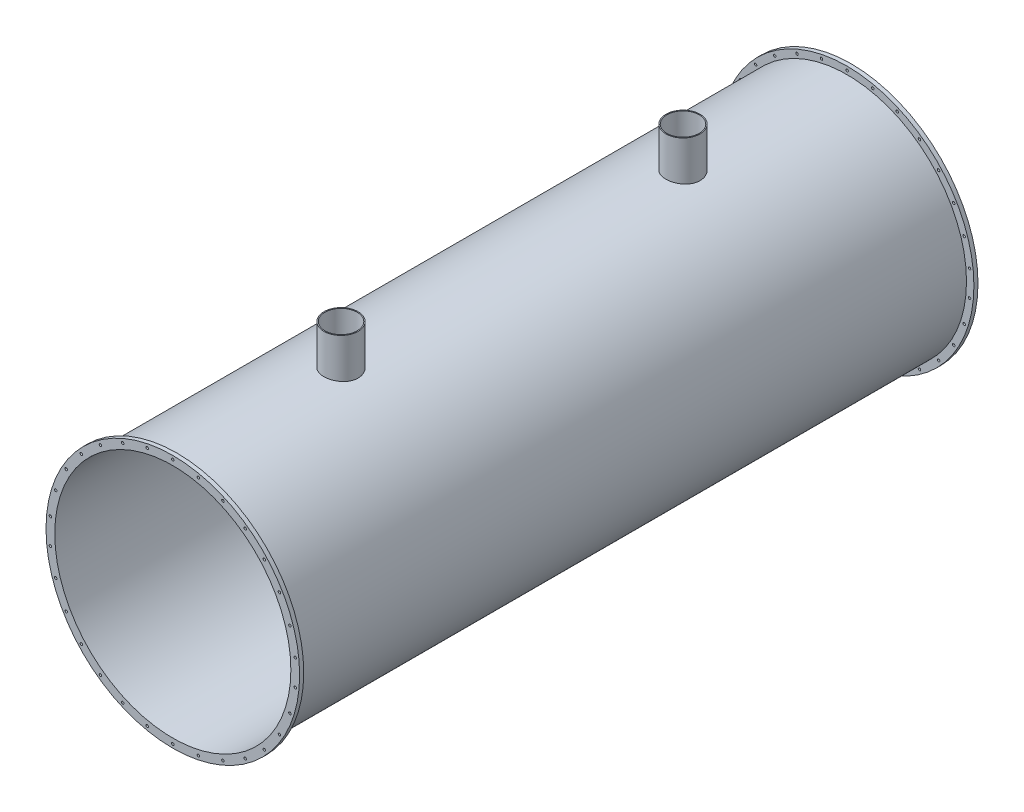
SolidWorks part; units mm, degrees
ref_plane "Front Plane" through (0, 0, 0) normal (0, 0, 1) x (1, 0, 0)
ref_plane "Top Plane" through (0, 0, 0) normal (0, 1, 0) x (1, 0, 0)
ref_plane "Right Plane" through (0, 0, 0) normal (1, 0, 0) x (0, 0, -1)
sketch "Sketch1" plane through (0, 0, 0) normal (0, 0, 1) x (1, 0, 0)
  circle A0 centre (0, 0) radius 2130.025
  circle A1 centre (0, 0) radius 2105.58
extrude "Boss-Extrude1" add sketch "Sketch1" along normal blind 12100
ref_plane "Plane1" through (0, 2830.0235, 0) normal (0, 1, 0) x (1, 0, 0)
sketch "Sketch2" plane through (0, 2830.0235, 0) normal (0, 1, 0) x (1, 0, 0)
  line L0 (2130.025, 0) -> (-2130.025, 0) construction
  line L1 (-2130.025, -12100) -> (2130.025, -12100) construction
  circle A0 centre (0, -3000) radius 304.8
  circle A1 centre (0, -9100) radius 304.8
  dimension "D1" = 609.6
  dimension "D3" = 3000
  dimension "D2" = 3000
extrude "Boss-Extrude2" add sketch "Sketch2" against normal up to surface up to face at (2130.025, 0, 12100)
sketch "Sketch3" plane through (0, 2830.0235, 0) normal (0, 1, 0) x (1, 0, 0)
  circle A0 centre (0, -9100) radius 287.4
  circle A1 centre (0, -3000) radius 287.4
  dimension "D1" = 574.8
extrude "Cut-Extrude1" cut sketch "Sketch3" against normal blind 1000
sketch "Sketch4" plane through (0, 0, 12100) normal (0, 0, 1) x (1, 0, 0)
  circle A0 centre (0, 0) radius 2262.0235
  circle A1 centre (0, 0) radius 2130.025 construction
  circle A2 centre (0, 0) radius 2130.025
  dimension "D1" = 4524.047
extrude "Boss-Extrude3" add sketch "Sketch4" against normal blind 73
sketch "Sketch5" plane through (0, 0, 12100) normal (0, 0, 1) x (1, 0, 0)
  circle A0 centre (0, 0) radius 2196.025 construction
  circle A1 centre (0, 2196.025) radius 22
  circle A2 centre (456.5793, 2148.0366) radius 22
  circle A3 centre (893.2038, 2006.1687) radius 22
  circle A4 centre (1290.7911, 1776.6215) radius 22
  circle A5 centre (1631.9646, 1469.4275) radius 22
  circle A6 centre (1901.8134, 1098.0125) radius 22
  circle A7 centre (2088.5439, 678.609) radius 22
  circle A8 centre (2183.9949, 229.5471) radius 22
  circle A9 centre (2183.9949, -229.5471) radius 22
  circle A10 centre (2088.5439, -678.609) radius 22
  circle A11 centre (1901.8134, -1098.0125) radius 22
  circle A12 centre (1631.9646, -1469.4275) radius 22
  circle A13 centre (1290.7911, -1776.6215) radius 22
  circle A14 centre (893.2038, -2006.1687) radius 22
  circle A15 centre (456.5793, -2148.0366) radius 22
  circle A16 centre (0, -2196.025) radius 22
  circle A17 centre (-456.5793, -2148.0366) radius 22
  circle A18 centre (-893.2038, -2006.1687) radius 22
  circle A19 centre (-1290.7911, -1776.6215) radius 22
  circle A20 centre (-1631.9646, -1469.4275) radius 22
  circle A21 centre (-1901.8134, -1098.0125) radius 22
  circle A22 centre (-2088.5439, -678.609) radius 22
  circle A23 centre (-2183.9949, -229.5471) radius 22
  circle A24 centre (-2183.9949, 229.5471) radius 22
  circle A25 centre (-2088.5439, 678.609) radius 22
  circle A26 centre (-1901.8134, 1098.0125) radius 22
  circle A27 centre (-1631.9646, 1469.4275) radius 22
  circle A28 centre (-1290.7911, 1776.6215) radius 22
  circle A29 centre (-893.2038, 2006.1687) radius 22
  circle A30 centre (-456.5793, 2148.0366) radius 22
  point P66 (0, 0)
  dimension "D1" = 44
  dimension "D2" = 4392.05
  dimension "D3" = 30
extrude "Cut-Extrude2" cut sketch "Sketch5" against normal up to next (73 mm away)
sketch "Sketch6" plane through (0, 0, 0) normal (0, 0, -1) x (-1, 0, 0)
  circle A1 centre (0, 0) radius 2130.025
  circle A2 centre (0, 0) radius 2130.025
  circle A3 centre (0, 0) radius 2262.0235
  circle A4 centre (0, 0) radius 2262.0235
  dimension "D1" = 0
  dimension "D2" = 0
extrude "Boss-Extrude4" add sketch "Sketch6" against normal blind 73
sketch "Sketch7" plane through (0, 0, 0) normal (0, 0, -1) x (-1, 0, 0)
  circle A1 centre (-1631.9646, 1469.4275) radius 22
  circle A2 centre (-1631.9646, 1469.4275) radius 22
  circle A3 centre (-1290.7911, 1776.6215) radius 22
  circle A4 centre (-1290.7911, 1776.6215) radius 22
  circle A5 centre (-893.2038, 2006.1687) radius 22
  circle A6 centre (-893.2038, 2006.1687) radius 22
  circle A7 centre (-456.5793, 2148.0366) radius 22
  circle A8 centre (-456.5793, 2148.0366) radius 22
  circle A9 centre (0, 2196.025) radius 22
  circle A10 centre (0, 2196.025) radius 22
  circle A11 centre (-1290.7911, -1776.6215) radius 22
  circle A12 centre (-1290.7911, -1776.6215) radius 22
  circle A13 centre (-1631.9646, -1469.4275) radius 22
  circle A14 centre (-1631.9646, -1469.4275) radius 22
  circle A15 centre (-1901.8134, -1098.0125) radius 22
  circle A16 centre (-1901.8134, -1098.0125) radius 22
  circle A17 centre (-2088.5439, -678.609) radius 22
  circle A18 centre (-2088.5439, -678.609) radius 22
  circle A19 centre (-2183.9949, -229.5471) radius 22
  circle A20 centre (-2183.9949, -229.5471) radius 22
  circle A21 centre (-2183.9949, 229.5471) radius 22
  circle A22 centre (-2183.9949, 229.5471) radius 22
  circle A23 centre (-2088.5439, 678.609) radius 22
  circle A24 centre (-2088.5439, 678.609) radius 22
  circle A25 centre (-1901.8134, 1098.0125) radius 22
  circle A26 centre (-1901.8134, 1098.0125) radius 22
  circle A27 centre (1901.8134, -1098.0125) radius 22
  circle A28 centre (1901.8134, -1098.0125) radius 22
  circle A29 centre (1631.9646, -1469.4275) radius 22
  circle A30 centre (1631.9646, -1469.4275) radius 22
  circle A31 centre (1290.7911, -1776.6215) radius 22
  circle A32 centre (1290.7911, -1776.6215) radius 22
  circle A33 centre (893.2038, -2006.1687) radius 22
  circle A34 centre (893.2038, -2006.1687) radius 22
  circle A35 centre (456.5793, -2148.0366) radius 22
  circle A36 centre (456.5793, -2148.0366) radius 22
  circle A37 centre (0, -2196.025) radius 22
  circle A38 centre (0, -2196.025) radius 22
  circle A39 centre (-456.5793, -2148.0366) radius 22
  circle A40 centre (-456.5793, -2148.0366) radius 22
  circle A41 centre (-893.2038, -2006.1687) radius 22
  circle A42 centre (-893.2038, -2006.1687) radius 22
  circle A43 centre (893.2038, 2006.1687) radius 22
  circle A44 centre (893.2038, 2006.1687) radius 22
  circle A45 centre (1290.7911, 1776.6215) radius 22
  circle A46 centre (1290.7911, 1776.6215) radius 22
  circle A47 centre (1631.9646, 1469.4275) radius 22
  circle A48 centre (1631.9646, 1469.4275) radius 22
  circle A49 centre (1901.8134, 1098.0125) radius 22
  circle A50 centre (1901.8134, 1098.0125) radius 22
  circle A51 centre (2088.5439, 678.609) radius 22
  circle A52 centre (2088.5439, 678.609) radius 22
  circle A53 centre (2183.9949, 229.5471) radius 22
  circle A54 centre (2183.9949, 229.5471) radius 22
  circle A55 centre (2183.9949, -229.5471) radius 22
  circle A56 centre (2183.9949, -229.5471) radius 22
  circle A57 centre (2088.5439, -678.609) radius 22
  circle A58 centre (2088.5439, -678.609) radius 22
  circle A59 centre (456.5793, 2148.0366) radius 22
  circle A60 centre (456.5793, 2148.0366) radius 22
  dimension "D1" = 0
  dimension "D2" = 0
  dimension "D3" = 0
  dimension "D4" = 0
  dimension "D5" = 0
  dimension "D6" = 0
  dimension "D7" = 0
  dimension "D8" = 0
  dimension "D9" = 0
  dimension "D10" = 0
  dimension "D11" = 0
  dimension "D12" = 0
  dimension "D13" = 0
  dimension "D14" = 0
  dimension "D15" = 0
  dimension "D16" = 0
  dimension "D17" = 0
  dimension "D18" = 0
  dimension "D19" = 0
  dimension "D20" = 0
  dimension "D21" = 0
  dimension "D22" = 0
  dimension "D23" = 0
  dimension "D24" = 0
  dimension "D25" = 0
  dimension "D26" = 0
  dimension "D27" = 0
  dimension "D28" = 0
  dimension "D29" = 0
  dimension "D30" = 0
extrude "Cut-Extrude3" cut sketch "Sketch7" against normal up to next (73 mm away)
